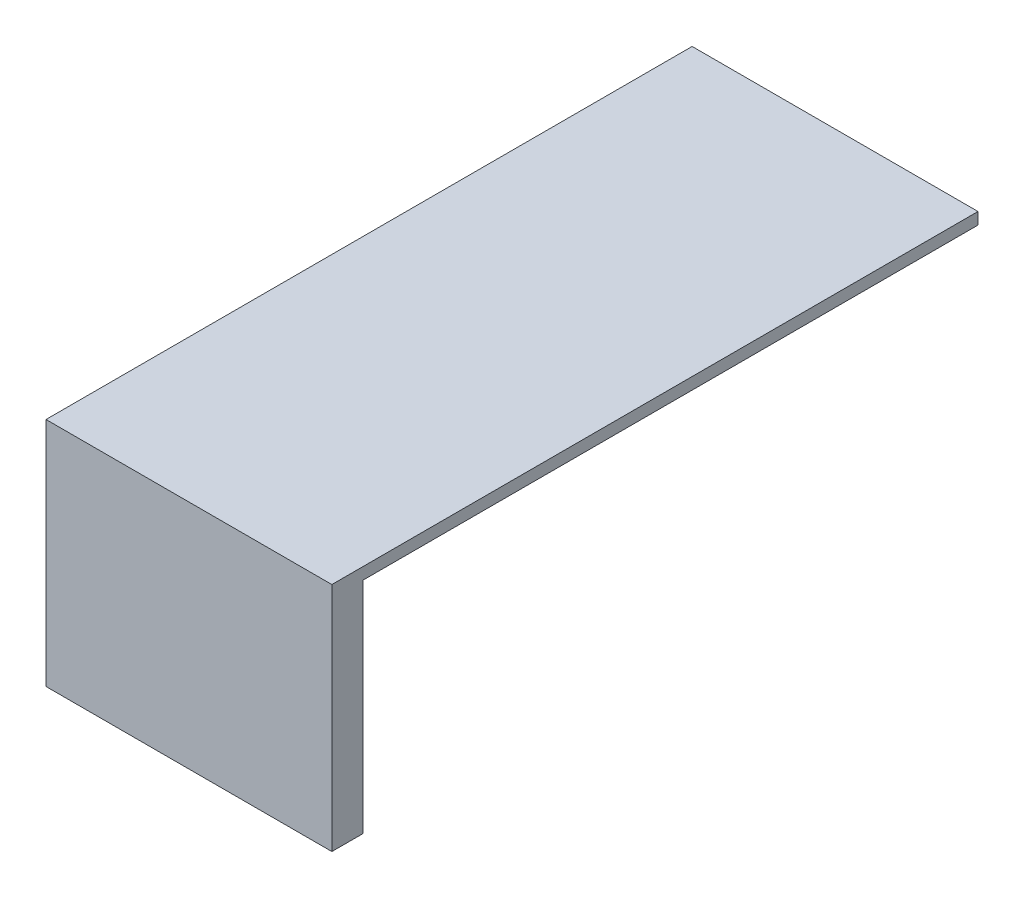
SolidWorks part; units mm, degrees
ref_plane "Front Plane" through (0, 0, 0) normal (0, 0, 1) x (1, 0, 0)
ref_plane "Top Plane" through (0, 0, 0) normal (0, 1, 0) x (1, 0, 0)
ref_plane "Right Plane" through (0, 0, 0) normal (1, 0, 0) x (0, 0, -1)
sketch "Sketch1" plane through (0, 0, 0) normal (0, 1, 0) x (1, 0, 0)
  circle A0 centre (0, 0) radius 28.1
extrude "Boss-Extrude1" add sketch "Sketch1" along normal blind 1
sketch "Sketch2" plane through (0, 1, 0) normal (0, 1, 0) x (1, 0, 0)
  circle A0 centre (0, -7) radius 18.6
extrude "Cut-Extrude1" cut sketch "Sketch2" against normal blind 58.8
sketch "Sketch3" plane through (0, 0, 0) normal (0, -1, 0) x (-1, 0, 0)
  line L1 (111.3415, -182.1414) -> (-111.3415, -182.1414)
  line L2 (111.3415, -182.1414) -> (111.3415, 182.1414)
  line L3 (111.3415, 182.1414) -> (-111.3415, 182.1414)
  line L4 (-111.3415, -182.1414) -> (-111.3415, 182.1414)
  line L5 (111.3415, -182.1414) -> (-111.3415, 182.1414) construction
  line L6 (111.3415, 182.1414) -> (-111.3415, -182.1414) construction
  point P0 (0, 0)
extrude "Boss-Extrude2" add sketch "Sketch3" along normal blind 58.8
sketch "Sketch4" plane through (0, -58.8, 0) normal (0, -1, 0) x (-1, 0, 0)
  line L1 (103.9587, -174.2721) -> (-103.9587, -174.2721)
  line L2 (103.9587, -174.2721) -> (103.9587, 174.2721)
  line L3 (103.9587, 174.2721) -> (-103.9587, 174.2721)
  line L4 (-103.9587, -174.2721) -> (-103.9587, 174.2721)
  line L5 (103.9587, -174.2721) -> (-103.9587, 174.2721) construction
  line L6 (103.9587, 174.2721) -> (-103.9587, -174.2721) construction
  point P0 (0, 0)
extrude "Cut-Extrude2" cut sketch "Sketch4" against normal blind 55.8
sketch "Sketch6" plane through (0, 1, 0) normal (0, 1, 0) x (1, 0, 0)
  circle A1 centre (0, 18.75) radius 3.75
sketch "Sketch9" plane through (0, 0, 0) normal (0, 1, 0) x (1, 0, 0)
  circle A1 centre (0, -7) radius 3
extrude "Cut-Extrude8" cut sketch "Sketch9" against normal blind 10
sketch "Sketch10" plane through (0, 1, 0) normal (0, 1, 0) x (1, 0, 0)
  circle A2 centre (0, 19.85) radius 3.75
extrude "Cut-Extrude9" cut sketch "Sketch10" against normal blind 10
sketch "Sketch11" plane through (0, -58.8, 0) normal (0, -1, 0) x (-1, 0, 0)
  line L0 (38.6585, -17.8586) -> (38.6585, -182.1414)
  line L23 (38.6585, -17.8586) -> (111.3415, -17.8586)
  line L26 (-111.3415, -182.1414) -> (111.3415, -182.1414) construction
  line L27 (38.6585, -182.1414) -> (-111.3415, -182.1414)
  line L28 (-111.3415, -182.1414) -> (-111.3415, 182.1414)
  line L29 (-111.3415, 182.1414) -> (111.3415, 182.1414)
  line L30 (111.3415, 182.1414) -> (111.3415, -17.8586)
extrude "Cut-Extrude13" cut sketch "Sketch11" against normal blind 500
extrude "Cut-Extrude5" cut sketch "Sketch6" against normal blind 400
sketch "Sketch8" plane through (0, 0, -182.1414) normal (0, 0, -1) x (-1, 0, 0)
  circle A0 centre (-86.5737, -25.0112) radius 10
extrude "Cut-Extrude7" cut sketch "Sketch8" against normal blind 10 contours A0
